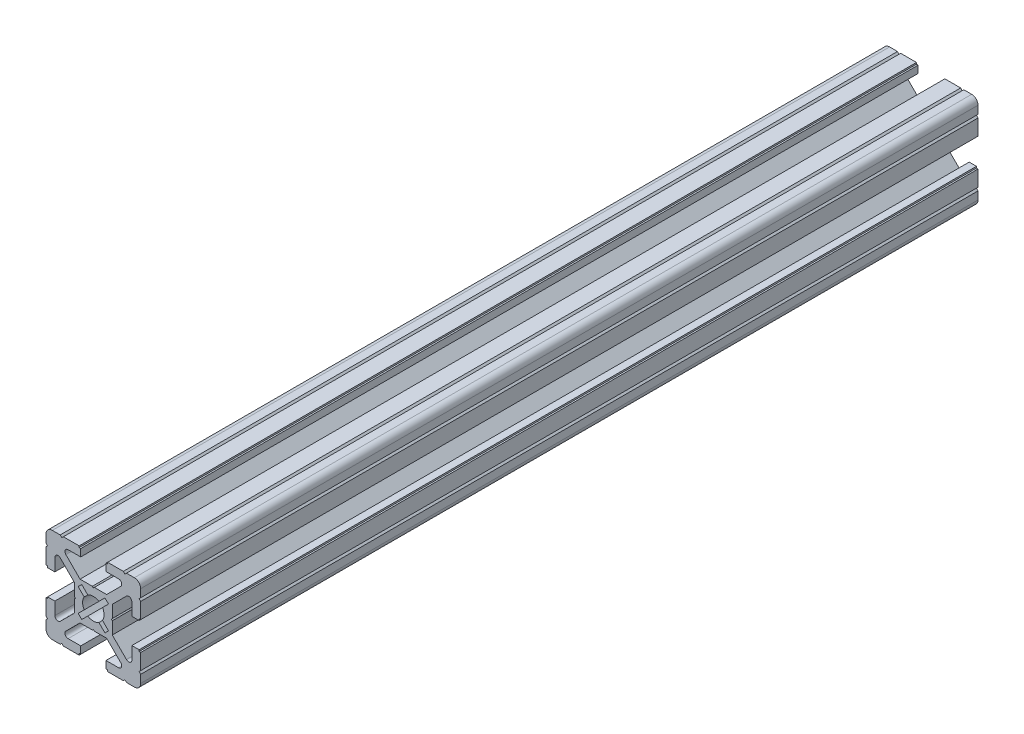
SolidWorks part; units mm, degrees
ref_plane "Front Plane" through (0, 0, 0) normal (0, 0, 1) x (1, 0, 0)
ref_plane "Top Plane" through (0, 0, 0) normal (0, 1, 0) x (1, 0, 0)
ref_plane "Right Plane" through (0, 0, 0) normal (1, 0, 0) x (0, 0, -1)
ref_plane "Plane1" through (0, 0, -65) normal (0, 0, -1) x (-1, 0, 0)
sketch "Sketch1" plane through (0, 0, -65) normal (0, 0, -1) x (-1, 0, 0)
  line L0 (4.8083, 3.677) -> (2.9023, 1.771)
  line L1 (2.9023, -1.771) -> (4.8083, -3.677)
  line L2 (4.8083, -3.677) -> (3.677, -4.8083)
  line L3 (3.677, -4.8083) -> (1.771, -2.9023)
  line L4 (-1.771, -2.9023) -> (-3.677, -4.8083)
  line L5 (-3.677, -4.8083) -> (-4.8083, -3.677)
  line L6 (-4.8083, -3.677) -> (-2.9023, -1.771)
  line L7 (-2.9023, 1.771) -> (-4.8083, 3.677)
  line L8 (-4.8083, 3.677) -> (-3.677, 4.8083)
  line L9 (-3.677, 4.8083) -> (-1.771, 2.9023)
  line L10 (1.771, 2.9023) -> (3.677, 4.8083)
  line L11 (3.677, 4.8083) -> (4.8083, 3.677)
  line L12 (-15, 13) -> (-15, 10.5)
  line L13 (-15, 10.5) -> (-14.5, 10)
  line L14 (-14.5, 10) -> (-15, 9.5)
  line L15 (-15, 9.5) -> (-15, 4.5)
  line L16 (-15, 4.5) -> (-14.5, 4.5)
  line L17 (-14.5, 4.5) -> (-14.5, 4)
  line L18 (-14.5, 4) -> (-12.2, 4)
  line L19 (-12.2, 4) -> (-12.2, 8)
  line L20 (-10.4929, 8.7071) -> (-6, 4.2142)
  line L21 (-6, 4.2142) -> (-6, 0.3125)
  line L22 (-6, 0.3125) -> (-5.7, 0)
  line L23 (-5.7, 0) -> (-6, -0.3125)
  line L24 (-6, -0.3125) -> (-6, -4.2142)
  line L25 (-6, -4.2142) -> (-10.4929, -8.7071)
  line L26 (-12.2, -8) -> (-12.2, -4)
  line L27 (-12.2, -4) -> (-14.5, -4)
  line L28 (-14.5, -4) -> (-14.5, -4.5)
  line L29 (-14.5, -4.5) -> (-15, -4.5)
  line L30 (-15, -4.5) -> (-15, -9.5)
  line L31 (-15, -9.5) -> (-14.5, -10)
  line L32 (-14.5, -10) -> (-15, -10.5)
  line L33 (-15, -10.5) -> (-15, -13)
  line L34 (-13, -15) -> (-10.5, -15)
  line L35 (-10.5, -15) -> (-10, -14.5)
  line L36 (-10, -14.5) -> (-9.5, -15)
  line L37 (-9.5, -15) -> (-4.5, -15)
  line L38 (-4.5, -15) -> (-4.5, -14.5)
  line L39 (-4.5, -14.5) -> (-4, -14.5)
  line L40 (-4, -14.5) -> (-4, -12.2)
  line L41 (-4, -12.2) -> (-8, -12.2)
  line L42 (-8.7071, -10.4929) -> (-4.2142, -6)
  line L43 (-4.2142, -6) -> (-0.3125, -6)
  line L44 (-0.3125, -6) -> (0, -5.7)
  line L45 (0, -5.7) -> (0.3125, -6)
  line L46 (0.3125, -6) -> (4.2142, -6)
  line L47 (4.2142, -6) -> (8.7071, -10.4929)
  line L48 (8, -12.2) -> (4, -12.2)
  line L49 (4, -12.2) -> (4, -14.5)
  line L50 (4, -14.5) -> (4.5, -14.5)
  line L51 (4.5, -14.5) -> (4.5, -15)
  line L52 (4.5, -15) -> (9.5, -15)
  line L53 (9.5, -15) -> (9.9899, -14.5)
  line L54 (9.9899, -14.5) -> (10.4899, -15)
  line L55 (10.4899, -15) -> (13, -15)
  line L56 (15, -13) -> (15, -10.5)
  line L57 (15, -10.5) -> (14.5, -10)
  line L58 (14.5, -10) -> (15, -9.5)
  line L59 (15, -9.5) -> (15, -4.5)
  line L60 (15, -4.5) -> (14.5, -4.5)
  line L61 (14.5, -4.5) -> (14.5, -4)
  line L62 (14.5, -4) -> (12.2, -4)
  line L63 (12.2, -4) -> (12.2, -8)
  line L64 (10.4929, -8.7071) -> (6, -4.2142)
  line L65 (6, -4.2142) -> (6, -0.3125)
  line L66 (6, -0.3125) -> (5.7, 0)
  line L67 (5.7, 0) -> (6, 0.3125)
  line L68 (6, 0.3125) -> (6, 4.2142)
  line L69 (6, 4.2142) -> (10.4929, 8.7071)
  line L70 (12.2, 8) -> (12.2, 4)
  line L71 (12.2, 4) -> (14.5, 4)
  line L72 (14.5, 4) -> (14.5, 4.5)
  line L73 (14.5, 4.5) -> (15, 4.5)
  line L74 (15, 4.5) -> (15, 9.5)
  line L75 (15, 9.5) -> (14.5, 10)
  line L76 (14.5, 10) -> (15, 10.5)
  line L77 (15, 10.5) -> (15, 13)
  line L78 (13, 15) -> (10.5, 15)
  line L79 (10.5, 15) -> (10, 14.5)
  line L80 (10, 14.5) -> (9.5, 15)
  line L81 (9.5, 15) -> (4.5, 15)
  line L82 (4.5, 15) -> (4.5, 14.5)
  line L83 (4.5, 14.5) -> (4, 14.5)
  line L84 (4, 14.5) -> (4, 12.2)
  line L85 (4, 12.2) -> (8, 12.2)
  line L86 (8.7071, 10.4929) -> (4.2142, 6)
  line L87 (4.2142, 6) -> (0.3125, 6)
  line L88 (0.3125, 6) -> (0, 5.7)
  line L89 (0, 5.7) -> (-0.3125, 6)
  line L90 (-0.3125, 6) -> (-4.2142, 6)
  line L91 (-4.2142, 6) -> (-8.7071, 10.4929)
  line L92 (-8, 12.2) -> (-4, 12.2)
  line L93 (-4, 12.2) -> (-4, 14.5)
  line L94 (-4, 14.5) -> (-4.5, 14.5)
  line L95 (-4.5, 14.5) -> (-4.5, 15)
  line L96 (-4.5, 15) -> (-9.5, 15)
  line L97 (-9.5, 15) -> (-10, 14.5)
  line L98 (-10, 14.5) -> (-10.5, 15)
  line L99 (-10.5, 15) -> (-13, 15)
  arc A0 (2.9023, 1.771) -> (2.9023, -1.771) centre (0, 0) cw
  arc A1 (1.771, -2.9023) -> (-1.771, -2.9023) centre (0, 0) cw
  arc A2 (-2.9023, -1.771) -> (-2.9023, 1.771) centre (0, 0) cw
  arc A3 (-1.771, 2.9023) -> (1.771, 2.9023) centre (0, 0) cw
  arc A4 (-13, 15) -> (-15, 13) centre (-13, 13) ccw
  arc A5 (-12.2, 8) -> (-10.4929, 8.7071) centre (-11.2, 8) cw
  arc A6 (-10.4929, -8.7071) -> (-12.2, -8) centre (-11.2, -8) cw
  arc A7 (-15, -13) -> (-13, -15) centre (-13, -13) ccw
  arc A8 (-8, -12.2) -> (-8.7071, -10.4929) centre (-8, -11.2) cw
  arc A9 (8.7071, -10.4929) -> (8, -12.2) centre (8, -11.2) cw
  arc A10 (13, -15) -> (15, -13) centre (13, -13) ccw
  arc A11 (12.2, -8) -> (10.4929, -8.7071) centre (11.2, -8) cw
  arc A12 (10.4929, 8.7071) -> (12.2, 8) centre (11.2, 8) cw
  arc A13 (15, 13) -> (13, 15) centre (13, 13) ccw
  arc A14 (8, 12.2) -> (8.7071, 10.4929) centre (8, 11.2) cw
  arc A15 (-8.7071, 10.4929) -> (-8, 12.2) centre (-8, 11.2) cw
extrude "Boss-Extrude1" add sketch "Sketch1" against normal blind 165
sketch "Sketch2" plane through (0, 0, 100) normal (0, 0, 1) x (1, 0, 0)
  line L0 (-1.771, 2.9023) -> (-3.677, 4.8083)
  line L1 (-3.677, 4.8083) -> (-4.8083, 3.677)
  line L2 (-4.8083, 3.677) -> (-2.9023, 1.771)
  line L3 (-3.677, 4.8083) -> (-1.771, 2.9023) construction
  line L4 (-4.8083, 3.677) -> (-3.677, 4.8083) construction
  line L5 (-2.9023, 1.771) -> (-4.8083, 3.677) construction
  line L6 (2.9023, 1.771) -> (4.8083, 3.677)
  line L7 (4.8083, 3.677) -> (3.677, 4.8083)
  line L8 (3.677, 4.8083) -> (1.771, 2.9023)
  line L9 (1.771, -2.9023) -> (3.677, -4.8083)
  line L10 (3.677, -4.8083) -> (4.8083, -3.677)
  line L11 (4.8083, -3.677) -> (2.9023, -1.771)
  line L12 (-2.9023, -1.771) -> (-4.8083, -3.677)
  line L13 (-4.8083, -3.677) -> (-3.677, -4.8083)
  line L14 (-3.677, -4.8083) -> (-1.771, -2.9023)
  line L15 (4.8083, 3.677) -> (2.9023, 1.771) construction
  line L16 (3.677, 4.8083) -> (4.8083, 3.677) construction
  line L88 (13, 15) -> (10.5, 15)
  line L89 (10.5, 15) -> (10, 14.5)
  line L90 (10, 14.5) -> (9.5, 15)
  line L91 (9.5, 15) -> (4.5, 15)
  line L92 (4.5, 15) -> (4.5, 14.5)
  line L93 (4.5, 14.5) -> (4, 14.5)
  line L94 (4, 14.5) -> (4, 12.2)
  line L95 (4, 12.2) -> (8, 12.2)
  line L96 (8.7071, 10.4929) -> (4.2142, 6)
  line L97 (4.2142, 6) -> (0.3125, 6)
  line L98 (0.3125, 6) -> (0, 5.7)
  line L99 (0, 5.7) -> (-0.3125, 6)
  line L100 (-0.3125, 6) -> (-4.2142, 6)
  line L101 (-4.2142, 6) -> (-8.7071, 10.4929)
  line L102 (-8, 12.2) -> (-4, 12.2)
  line L103 (-4, 12.2) -> (-4, 14.5)
  line L104 (-4, 14.5) -> (-4.5, 14.5)
  line L105 (-4.5, 14.5) -> (-4.5, 15)
  line L106 (-4.5, 15) -> (-9.5, 15)
  line L107 (-9.5, 15) -> (-10, 14.5)
  line L108 (-10, 14.5) -> (-10.5, 15)
  line L109 (-10.5, 15) -> (-13, 15)
  line L110 (-15, 13) -> (-15, 10.5)
  line L111 (-15, 10.5) -> (-14.5, 10)
  line L112 (-14.5, 10) -> (-15, 9.5)
  line L113 (-15, 9.5) -> (-15, 4.5)
  line L114 (-15, 4.5) -> (-14.5, 4.5)
  line L115 (-14.5, 4.5) -> (-14.5, 4)
  line L116 (-14.5, 4) -> (-12.2, 4)
  line L117 (-12.2, 4) -> (-12.2, 8)
  line L118 (-10.4929, 8.7071) -> (-6, 4.2142)
  line L119 (-6, 4.2142) -> (-6, 0.3125)
  line L120 (-6, 0.3125) -> (-5.7, 0)
  line L121 (-5.7, 0) -> (-6, -0.3125)
  line L122 (-6, -0.3125) -> (-6, -4.2142)
  line L123 (-6, -4.2142) -> (-10.4929, -8.7071)
  line L124 (-12.2, -8) -> (-12.2, -4)
  line L125 (-12.2, -4) -> (-14.5, -4)
  line L126 (-14.5, -4) -> (-14.5, -4.5)
  line L127 (-14.5, -4.5) -> (-15, -4.5)
  line L128 (-15, -4.5) -> (-15, -9.5)
  line L129 (-15, -9.5) -> (-14.5, -10)
  line L130 (-14.5, -10) -> (-15, -10.5)
  line L131 (-15, -10.5) -> (-15, -13)
  line L132 (-13, -15) -> (-10.4899, -15)
  line L133 (-10.4899, -15) -> (-9.9899, -14.5)
  line L134 (-9.9899, -14.5) -> (-9.5, -15)
  line L135 (-9.5, -15) -> (-4.5, -15)
  line L136 (-4.5, -15) -> (-4.5, -14.5)
  line L137 (-4.5, -14.5) -> (-4, -14.5)
  line L138 (-4, -14.5) -> (-4, -12.2)
  line L139 (-4, -12.2) -> (-8, -12.2)
  line L140 (-8.7071, -10.4929) -> (-4.2142, -6)
  line L141 (-4.2142, -6) -> (-0.3125, -6)
  line L142 (-0.3125, -6) -> (0, -5.7)
  line L143 (0, -5.7) -> (0.3125, -6)
  line L144 (0.3125, -6) -> (4.2142, -6)
  line L145 (4.2142, -6) -> (8.7071, -10.4929)
  line L146 (8, -12.2) -> (4, -12.2)
  line L147 (4, -12.2) -> (4, -14.5)
  line L148 (4, -14.5) -> (4.5, -14.5)
  line L149 (4.5, -14.5) -> (4.5, -15)
  line L150 (4.5, -15) -> (9.5, -15)
  line L151 (9.5, -15) -> (10, -14.5)
  line L152 (10, -14.5) -> (10.5, -15)
  line L153 (10.5, -15) -> (13, -15)
  line L154 (15, -13) -> (15, -10.5)
  line L155 (15, -10.5) -> (14.5, -10)
  line L156 (14.5, -10) -> (15, -9.5)
  line L157 (15, -9.5) -> (15, -4.5)
  line L158 (15, -4.5) -> (14.5, -4.5)
  line L159 (14.5, -4.5) -> (14.5, -4)
  line L160 (14.5, -4) -> (12.2, -4)
  line L161 (12.2, -4) -> (12.2, -8)
  line L162 (10.4929, -8.7071) -> (6, -4.2142)
  line L163 (6, -4.2142) -> (6, -0.3125)
  line L164 (6, -0.3125) -> (5.7, 0)
  line L165 (5.7, 0) -> (6, 0.3125)
  line L166 (6, 0.3125) -> (6, 4.2142)
  line L167 (6, 4.2142) -> (10.4929, 8.7071)
  line L168 (12.2, 8) -> (12.2, 4)
  line L169 (12.2, 4) -> (14.5, 4)
  line L170 (14.5, 4) -> (14.5, 4.5)
  line L171 (14.5, 4.5) -> (15, 4.5)
  line L172 (15, 4.5) -> (15, 9.5)
  line L173 (15, 9.5) -> (14.5, 10)
  line L174 (14.5, 10) -> (15, 10.5)
  line L175 (15, 10.5) -> (15, 13)
  line L176 (13, 15) -> (10.5, 15)
  line L177 (10.5, 15) -> (10, 14.5)
  line L178 (10, 14.5) -> (9.5, 15)
  line L179 (9.5, 15) -> (4.5, 15)
  line L180 (4.5, 15) -> (4.5, 14.5)
  line L181 (4.5, 14.5) -> (4, 14.5)
  line L182 (4, 14.5) -> (4, 12.2)
  line L183 (4, 12.2) -> (8, 12.2)
  line L184 (8.7071, 10.4929) -> (4.2142, 6)
  line L185 (4.2142, 6) -> (0.3125, 6)
  line L186 (0.3125, 6) -> (0, 5.7)
  line L187 (0, 5.7) -> (-0.3125, 6)
  line L188 (-0.3125, 6) -> (-4.2142, 6)
  line L189 (-4.2142, 6) -> (-8.7071, 10.4929)
  line L190 (-8, 12.2) -> (-4, 12.2)
  line L191 (-4, 12.2) -> (-4, 14.5)
  line L192 (-4, 14.5) -> (-4.5, 14.5)
  line L193 (-4.5, 14.5) -> (-4.5, 15)
  line L194 (-4.5, 15) -> (-9.5, 15)
  line L195 (-9.5, 15) -> (-10, 14.5)
  line L196 (-10, 14.5) -> (-10.5, 15)
  line L197 (-10.5, 15) -> (-13, 15)
  line L198 (-15, 13) -> (-15, 10.5)
  line L199 (-15, 10.5) -> (-14.5, 10)
  line L200 (-14.5, 10) -> (-15, 9.5)
  line L201 (-15, 9.5) -> (-15, 4.5)
  line L202 (-15, 4.5) -> (-14.5, 4.5)
  line L203 (-14.5, 4.5) -> (-14.5, 4)
  line L204 (-14.5, 4) -> (-12.2, 4)
  line L205 (-12.2, 4) -> (-12.2, 8)
  line L206 (-10.4929, 8.7071) -> (-6, 4.2142)
  line L207 (-6, 4.2142) -> (-6, 0.3125)
  line L208 (-6, 0.3125) -> (-5.7, 0)
  line L209 (-5.7, 0) -> (-6, -0.3125)
  line L210 (-6, -0.3125) -> (-6, -4.2142)
  line L211 (-6, -4.2142) -> (-10.4929, -8.7071)
  line L212 (-12.2, -8) -> (-12.2, -4)
  line L213 (-12.2, -4) -> (-14.5, -4)
  line L214 (-14.5, -4) -> (-14.5, -4.5)
  line L215 (-14.5, -4.5) -> (-15, -4.5)
  line L216 (-15, -4.5) -> (-15, -9.5)
  line L217 (-15, -9.5) -> (-14.5, -10)
  line L218 (-14.5, -10) -> (-15, -10.5)
  line L219 (-15, -10.5) -> (-15, -13)
  line L220 (-13, -15) -> (-10.4899, -15)
  line L221 (-10.4899, -15) -> (-9.9899, -14.5)
  line L222 (-9.9899, -14.5) -> (-9.5, -15)
  line L223 (-9.5, -15) -> (-4.5, -15)
  line L224 (-4.5, -15) -> (-4.5, -14.5)
  line L225 (-4.5, -14.5) -> (-4, -14.5)
  line L226 (-4, -14.5) -> (-4, -12.2)
  line L227 (-4, -12.2) -> (-8, -12.2)
  line L228 (-8.7071, -10.4929) -> (-4.2142, -6)
  line L229 (-4.2142, -6) -> (-0.3125, -6)
  line L230 (-0.3125, -6) -> (0, -5.7)
  line L231 (0, -5.7) -> (0.3125, -6)
  line L232 (0.3125, -6) -> (4.2142, -6)
  line L233 (4.2142, -6) -> (8.7071, -10.4929)
  line L234 (8, -12.2) -> (4, -12.2)
  line L235 (4, -12.2) -> (4, -14.5)
  line L236 (4, -14.5) -> (4.5, -14.5)
  line L237 (4.5, -14.5) -> (4.5, -15)
  line L238 (4.5, -15) -> (9.5, -15)
  line L239 (9.5, -15) -> (10, -14.5)
  line L240 (10, -14.5) -> (10.5, -15)
  line L241 (10.5, -15) -> (13, -15)
  line L242 (15, -13) -> (15, -10.5)
  line L243 (15, -10.5) -> (14.5, -10)
  line L244 (14.5, -10) -> (15, -9.5)
  line L245 (15, -9.5) -> (15, -4.5)
  line L246 (15, -4.5) -> (14.5, -4.5)
  line L247 (14.5, -4.5) -> (14.5, -4)
  line L248 (14.5, -4) -> (12.2, -4)
  line L249 (12.2, -4) -> (12.2, -8)
  line L250 (10.4929, -8.7071) -> (6, -4.2142)
  line L251 (6, -4.2142) -> (6, -0.3125)
  line L252 (6, -0.3125) -> (5.7, 0)
  line L253 (5.7, 0) -> (6, 0.3125)
  line L254 (6, 0.3125) -> (6, 4.2142)
  line L255 (6, 4.2142) -> (10.4929, 8.7071)
  line L256 (12.2, 8) -> (12.2, 4)
  line L257 (12.2, 4) -> (14.5, 4)
  line L258 (14.5, 4) -> (14.5, 4.5)
  line L259 (14.5, 4.5) -> (15, 4.5)
  line L260 (15, 4.5) -> (15, 9.5)
  line L261 (15, 9.5) -> (14.5, 10)
  line L262 (14.5, 10) -> (15, 10.5)
  line L263 (15, 10.5) -> (15, 13)
  arc A0 (1.771, 2.9023) -> (-1.771, 2.9023) centre (0, 0) ccw
  arc A1 (1.771, 2.9023) -> (-1.771, 2.9023) centre (0, 0) ccw construction
  arc A2 (-2.9023, 1.771) -> (-2.9023, -1.771) centre (0, 0) ccw
  arc A3 (-1.771, -2.9023) -> (1.771, -2.9023) centre (0, 0) ccw
  arc A4 (2.9023, -1.771) -> (2.9023, 1.771) centre (0, 0) ccw
  arc A12 (15, 13) -> (13, 15) centre (13, 13) ccw
  arc A13 (8.7071, 10.4929) -> (8, 12.2) centre (8, 11.2) ccw
  arc A14 (-8, 12.2) -> (-8.7071, 10.4929) centre (-8, 11.2) ccw
  arc A15 (-13, 15) -> (-15, 13) centre (-13, 13) ccw
  arc A16 (-10.4929, 8.7071) -> (-12.2, 8) centre (-11.2, 8) ccw
  arc A17 (-12.2, -8) -> (-10.4929, -8.7071) centre (-11.2, -8) ccw
  arc A18 (-15, -13) -> (-13, -15) centre (-13, -13) ccw
  arc A19 (-8.7071, -10.4929) -> (-8, -12.2) centre (-8, -11.2) ccw
  arc A20 (8, -12.2) -> (8.7071, -10.4929) centre (8, -11.2) ccw
  arc A21 (13, -15) -> (15, -13) centre (13, -13) ccw
  arc A22 (10.4929, -8.7071) -> (12.2, -8) centre (11.2, -8) ccw
  arc A23 (12.2, 8) -> (10.4929, 8.7071) centre (11.2, 8) ccw
  arc A24 (15, 13) -> (13, 15) centre (13, 13) ccw
  arc A25 (8.7071, 10.4929) -> (8, 12.2) centre (8, 11.2) ccw
  arc A26 (-8, 12.2) -> (-8.7071, 10.4929) centre (-8, 11.2) ccw
  arc A27 (-13, 15) -> (-15, 13) centre (-13, 13) ccw
  arc A28 (-10.4929, 8.7071) -> (-12.2, 8) centre (-11.2, 8) ccw
  arc A29 (-12.2, -8) -> (-10.4929, -8.7071) centre (-11.2, -8) ccw
  arc A30 (-15, -13) -> (-13, -15) centre (-13, -13) ccw
  arc A31 (-8.7071, -10.4929) -> (-8, -12.2) centre (-8, -11.2) ccw
  arc A32 (8, -12.2) -> (8.7071, -10.4929) centre (8, -11.2) ccw
  arc A33 (13, -15) -> (15, -13) centre (13, -13) ccw
  arc A34 (10.4929, -8.7071) -> (12.2, -8) centre (11.2, -8) ccw
  arc A35 (12.2, 8) -> (10.4929, 8.7071) centre (11.2, 8) ccw
  point P81 (0, 0)
  dimension "D1" = 0
  dimension "D2" = 4
extrude "Boss-Extrude2" add sketch "Sketch2" along normal blind 100.28
